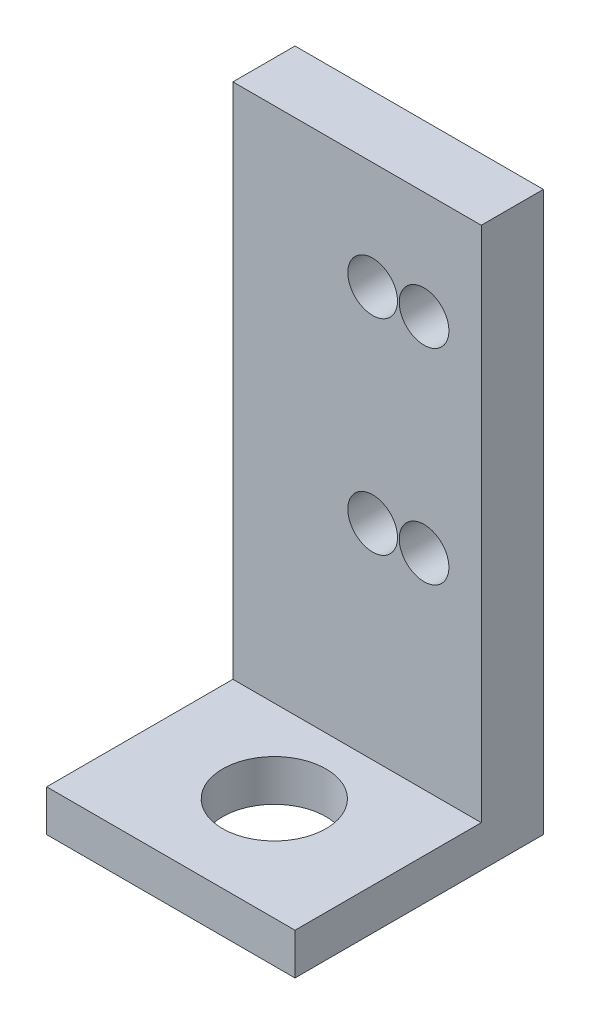
SolidWorks part; units mm, degrees
ref_plane "Front Plane" through (0, 0, 0) normal (0, 0, 1) x (1, 0, 0)
ref_plane "Top Plane" through (0, 0, 0) normal (0, 1, 0) x (1, 0, 0)
ref_plane "Right Plane" through (0, 0, 0) normal (1, 0, 0) x (0, 0, -1)
sketch "Sketch1" plane through (0, 0, 0) normal (0, 0, 1) x (1, 0, 0)
  line L1 (0, 0) -> (12, 0)
  line L2 (0, 0) -> (0, 27)
  line L3 (0, 27) -> (12, 27)
  line L4 (12, 0) -> (12, 27)
extrude "Boss-Extrude1" add sketch "Sketch1" along normal blind 3
sketch "Sketch2" plane through (0, 0, 3) normal (0, 0, 1) x (1, 0, 0)
  line L0 (12, 0) -> (12, 27) construction
  line L1 (0, 0) -> (12, 0)
  line L2 (0, 0) -> (0, 2)
  line L3 (0, 2) -> (12, 2)
  line L4 (12, 0) -> (12, 2)
extrude "Boss-Extrude2" add sketch "Sketch2" along normal blind 9
sketch "Sketch3" plane through (0, 2, 0) normal (0, 1, 0) x (1, 0, 0)
  circle A0 centre (6, -7) radius 2.5
extrude "Cut-Extrude1" cut sketch "Sketch3" against normal blind 10
sketch "Sketch4" plane through (0, 0, 3) normal (0, 0, 1) x (1, 0, 0)
  circle A0 centre (9.2361, 11.9) radius 1.2
  circle A1 centre (9.2361, 21.8) radius 1.2
extrude "Cut-Extrude2" cut sketch "Sketch4" against normal blind 10
sketch "Sketch5" plane through (0, 0, 3) normal (0, 0, 1) x (1, 0, 0)
  circle A0 centre (6.7522, 11.9) radius 1.2
  circle A1 centre (6.7522, 21.8) radius 1.2
extrude "Cut-Extrude3" cut sketch "Sketch5" against normal blind 10
